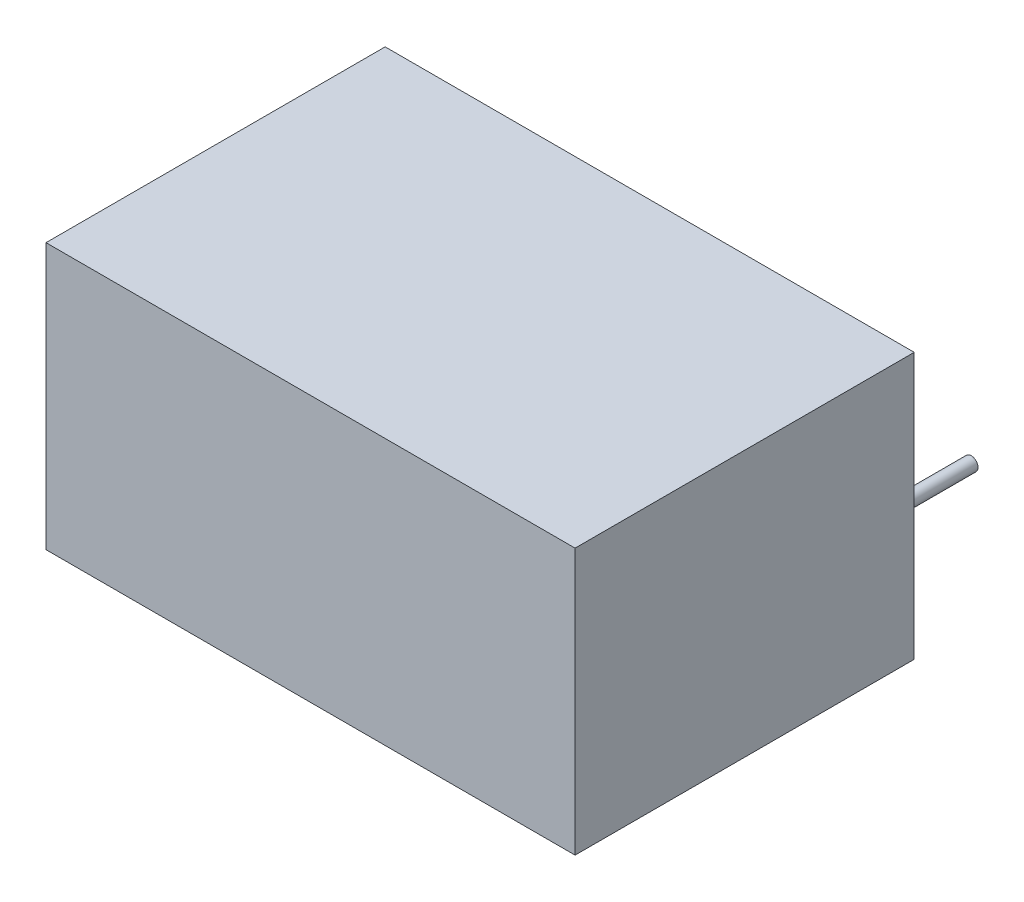
SolidWorks part; units mm, degrees
ref_plane "Front Plane" through (0, 0, 0) normal (0, 0, 1) x (1, 0, 0)
ref_plane "Top Plane" through (0, 0, 0) normal (0, 1, 0) x (1, 0, 0)
ref_plane "Right Plane" through (0, 0, 0) normal (1, 0, 0) x (0, 0, -1)
sketch "Sketch1" plane through (0, 0, 0) normal (0, 0, 1) x (1, 0, 0)
  line L1 (-9.75, 4.9) -> (9.75, 4.9)
  line L2 (-9.75, 4.9) -> (-9.75, -4.9)
  line L3 (-9.75, -4.9) -> (9.75, -4.9)
  line L4 (9.75, 4.9) -> (9.75, -4.9)
  line L5 (-9.75, 4.9) -> (9.75, -4.9) construction
  line L6 (-9.75, -4.9) -> (9.75, 4.9) construction
  point P0 (0, 0)
  dimension "D1" = 19.5
  dimension "D2" = 9.8
extrude "Boss-Extrude1" add sketch "Sketch1" along normal blind 12.5
sketch "Sketch2" plane through (0, 0, 0) normal (0, 0, -1) x (-1, 0, 0)
  line L0 (-7.75, -1.7) -> (11.1386, -1.7) construction
  line L1 (9.75, -4.9) -> (-9.75, -4.9) construction
  line L2 (-9.75, -4.9) -> (-9.75, 4.9) construction
  circle A0 centre (-7.75, -1.7) radius 0.25
  circle A1 centre (-5.21, -1.7) radius 0.25
  circle A2 centre (2.41, -1.7) radius 0.25
  circle A4 centre (7.49, -1.7) radius 0.25
  dimension "D6" = 0.5
  dimension "D1" = 2.54
  dimension "D2" = 7.62
  dimension "D3" = 5.08
  dimension "D4" = 3.2
  dimension "D5" = 2
extrude "Boss-Extrude2" add sketch "Sketch2" along normal blind 4.1
sketch "Sketch3" plane through (0, -4.9, 0) normal (0, -1, 0) x (1, 0, 0)
  text T0 "CUI" font "Century Gothic" height 5.08
extrude "Cut-Extrude1" cut sketch "Sketch3" against normal blind 0.0254
